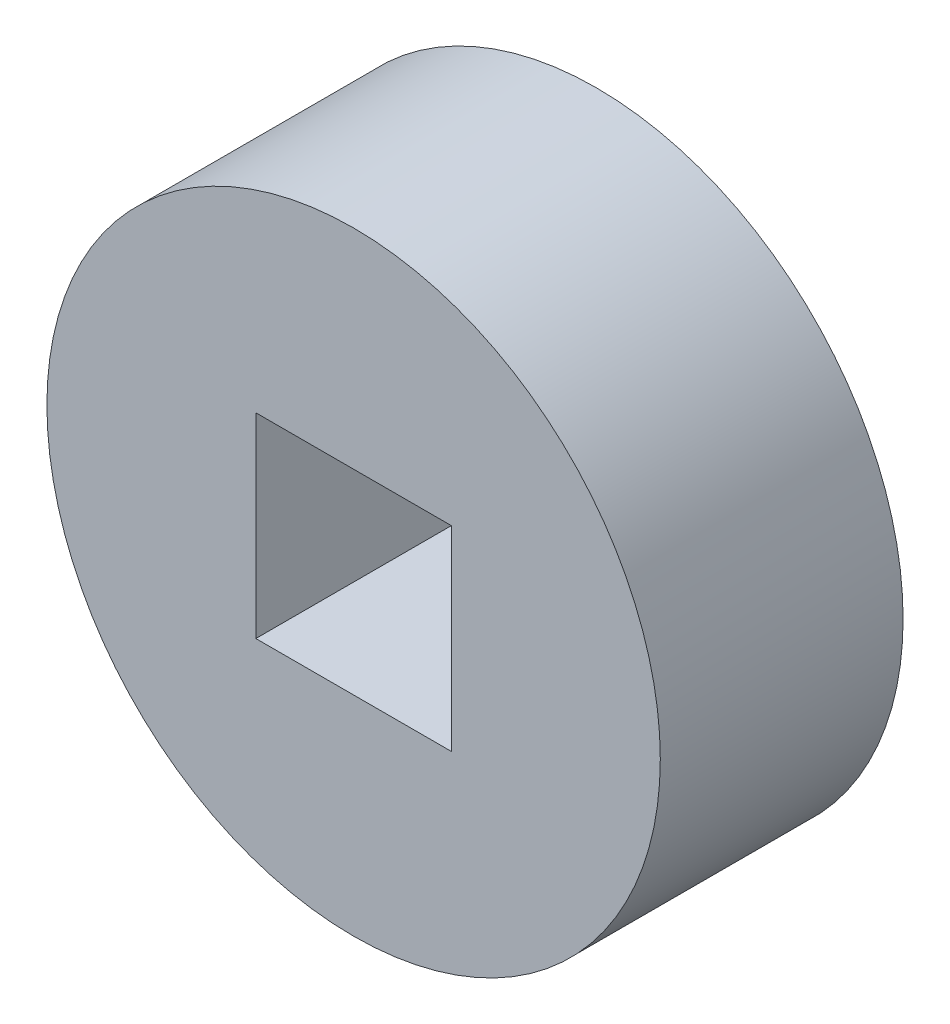
SolidWorks part; units mm, degrees
ref_plane "Ebene vorne" through (0, 0, 0) normal (0, 0, 1) x (1, 0, 0)
ref_plane "Ebene oben" through (0, 0, 0) normal (0, 1, 0) x (1, 0, 0)
ref_plane "Ebene rechts" through (0, 0, 0) normal (1, 0, 0) x (0, 0, -1)
sketch "Sketch1" plane through (0, 0, 0) normal (0, 0, 1) x (1, 0, 0)
  circle A0 centre (0, 0) radius 8
  dimension "D1" = 16
extrude "Boss-Extrude1" add sketch "Sketch1" against normal blind 6.333 from offset 8
sketch "Sketch3" plane through (0, 0, 0) normal (0, 0, 1) x (1, 0, 0)
  line L1 (-2.55, -2.55) -> (2.55, -2.55)
  line L2 (-2.55, -2.55) -> (-2.55, 2.55)
  line L3 (-2.55, 2.55) -> (2.55, 2.55)
  line L4 (2.55, -2.55) -> (2.55, 2.55)
  line L5 (-2.55, -2.55) -> (2.55, 2.55) construction
  line L6 (-2.55, 2.55) -> (2.55, -2.55) construction
  point P0 (0, 0)
  dimension "D1" = 5.1
  dimension "D2" = 5.1
extrude "Cut-Extrude4" cut sketch "Sketch3" along normal through all
